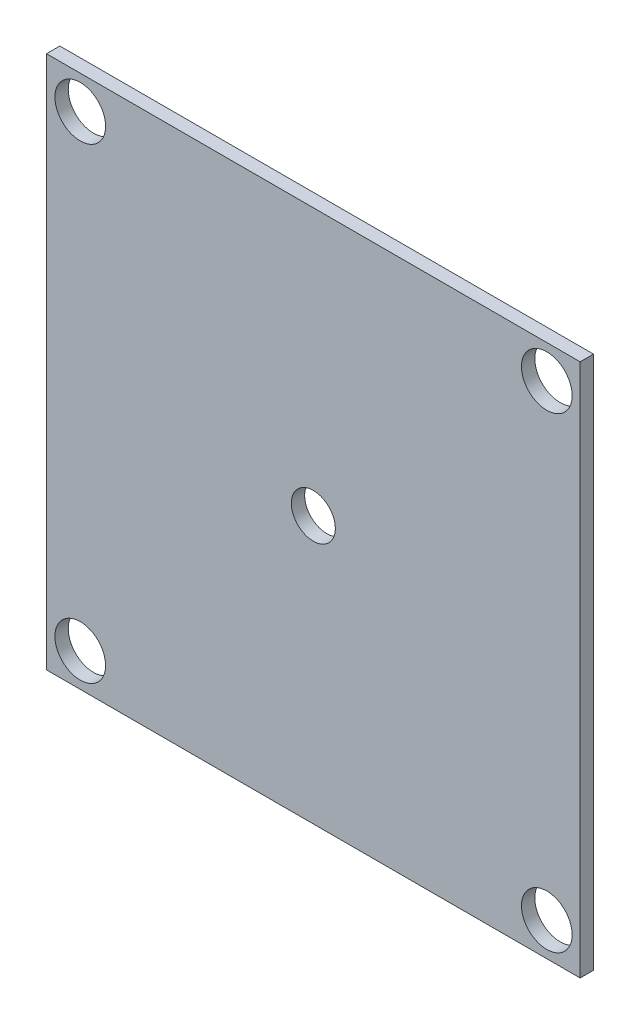
SolidWorks part; units mm, degrees
ref_plane "Front Plane" through (0, 0, 0) normal (0, 0, 1) x (1, 0, 0)
ref_plane "Top Plane" through (0, 0, 0) normal (0, 1, 0) x (1, 0, 0)
ref_plane "Right Plane" through (0, 0, 0) normal (1, 0, 0) x (0, 0, -1)
sketch "Sketch1" plane through (0, 0, 0) normal (0, 0, 1) x (1, 0, 0)
  line L1 (-50.8, -50.8) -> (50.8, -50.8)
  line L2 (-50.8, -50.8) -> (-50.8, 50.8)
  line L3 (-50.8, 50.8) -> (50.8, 50.8)
  line L4 (50.8, -50.8) -> (50.8, 50.8)
  line L5 (-50.8, -50.8) -> (50.8, 50.8) construction
  line L6 (-50.8, 50.8) -> (50.8, -50.8) construction
  point P0 (0, 0)
  dimension "D1" = 101.6
  dimension "D2" = 101.6
extrude "Boss-Extrude1" add sketch "Sketch1" along normal blind 2.54
sketch "Sketch2" plane through (0, 0, 0) normal (0, 0, -1) x (-1, 0, 0)
  line L0 (0, 50.8) -> (0, -50.8) construction
  line L1 (-50.8, 50.8) -> (50.8, 50.8) construction
  line L2 (50.8, -50.8) -> (-50.8, -50.8) construction
  line L3 (50.8, 50.8) -> (50.8, -50.8) construction
  line L4 (-50.8, -50.8) -> (-50.8, 50.8) construction
  line L5 (-50.8, 50.8) -> (50.8, 50.8) construction
  line L7 (50.8, -50.8) -> (-50.8, -50.8) construction
  circle A0 centre (-44.45, 44.45) radius 4.826
  circle A1 centre (44.3773, 44.45) radius 4.826
  circle A2 centre (44.3773, -44.45) radius 4.826
  circle A3 centre (-44.45, -44.45) radius 4.826
  dimension "D1" = 9.652
  dimension "D2" = 9.652
  dimension "D3" = 9.652
  dimension "D4" = 9.652
  dimension "D5" = 6.4227
  dimension "D6" = 6.4227
  dimension "D7" = 6.35
  dimension "D8" = 6.35
  dimension "D9" = 6.35
  dimension "D10" = 6.35
  dimension "D11" = 6.35
  dimension "D12" = 6.35
sketch "Sketch3" plane through (0, 0, 2.54) normal (0, 0, 1) x (1, 0, 0)
  circle A0 centre (0, 0) radius 4.191
  dimension "D1" = 8.382
extrude "Cut-Extrude1" cut sketch "Sketch3" against normal blind 635
extrude "Cut-Extrude6" cut sketch "Sketch2" against normal blind 2.54 contours A2 | A1 | A0 | A3
